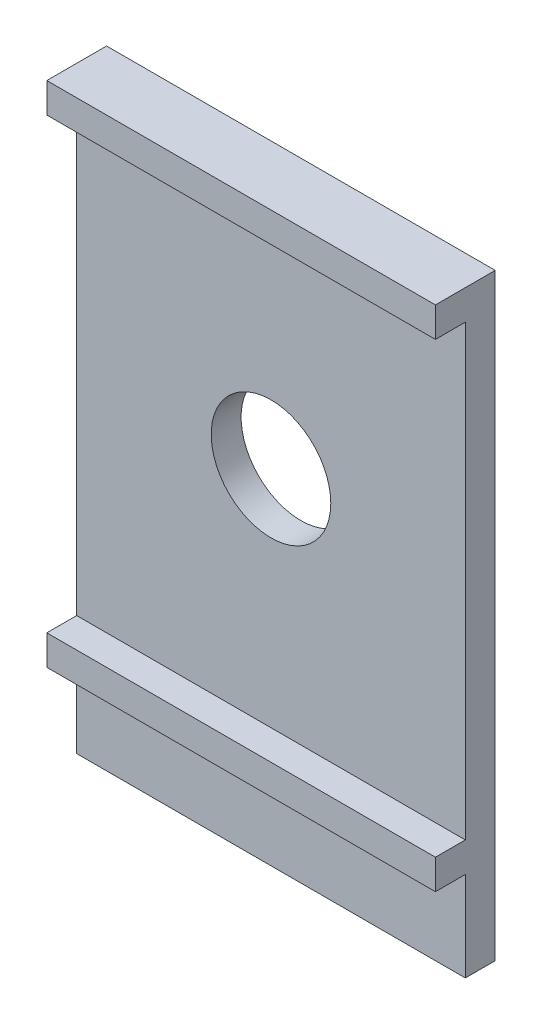
SolidWorks part; units mm, degrees
ref_plane "Přední rovina" through (0, 0, 0) normal (0, 0, 1) x (1, 0, 0)
ref_plane "Horní rovina" through (0, 0, 0) normal (0, 1, 0) x (1, 0, 0)
ref_plane "Pravá rovina" through (0, 0, 0) normal (1, 0, 0) x (0, 0, -1)
sketch "Skica1" plane through (0, 0, 0) normal (0, 0, 1) x (1, 0, 0)
  line L1 (0, 0) -> (13, 0)
  line L2 (0, 0) -> (0, 23.5)
  line L3 (0, 23.5) -> (13, 23.5)
  line L4 (13, 0) -> (13, 23.5)
  dimension "D1" = 13
  dimension "D2" = 23.5
extrude "Přidat vysunutím1" add sketch "Skica1" along normal blind 1
sketch "Skica2" plane through (0, 0, 1) normal (0, 0, 1) x (1, 0, 0)
  line L0 (13, 0) -> (13, 23.5) construction
  line L1 (0, 23.5) -> (13, 23.5)
  line L2 (0, 23.5) -> (0, 22.5)
  line L3 (0, 22.5) -> (13, 22.5)
  line L4 (13, 23.5) -> (13, 22.5)
  line L5 (0, 23.5) -> (0, 0) construction
  line L6 (0, 7.5) -> (13, 7.5)
  line L7 (0, 7.5) -> (0, 6.5)
  line L8 (0, 6.5) -> (13, 6.5)
  line L9 (13, 7.5) -> (13, 6.5)
  dimension "D1" = 1
  dimension "D2" = 1
  dimension "D3" = 15
extrude "Přidat vysunutím2" add sketch "Skica2" along normal blind 1
sketch "Skica3" plane through (0, 0, 1) normal (0, 0, 1) x (1, 0, 0)
  line L0 (13, 7.5) -> (0, 7.5) construction
  line L3 (0, 22.5) -> (0, 7.5) construction
  circle A0 centre (6.5, 15) radius 2
  dimension "D1" = 4
  dimension "D2" = 7.5
  dimension "D3" = 6.5
extrude "Odebrat vysunutím1" cut sketch "Skica3" against normal blind 1
sketch "Skica4" plane through (0, 0, 1) normal (0, 0, 1) x (1, 0, 0)
  line L0 (13, 0) -> (13, 6.5) construction
  line L1 (0, 0) -> (13, 0)
  line L2 (0, 0) -> (0, 3.5)
  line L3 (0, 3.5) -> (13, 3.5)
  line L4 (13, 0) -> (13, 3.5)
  dimension "D1" = 3.5
extrude "Odebrat vysunutím2" cut sketch "Skica4" against normal blind 10
